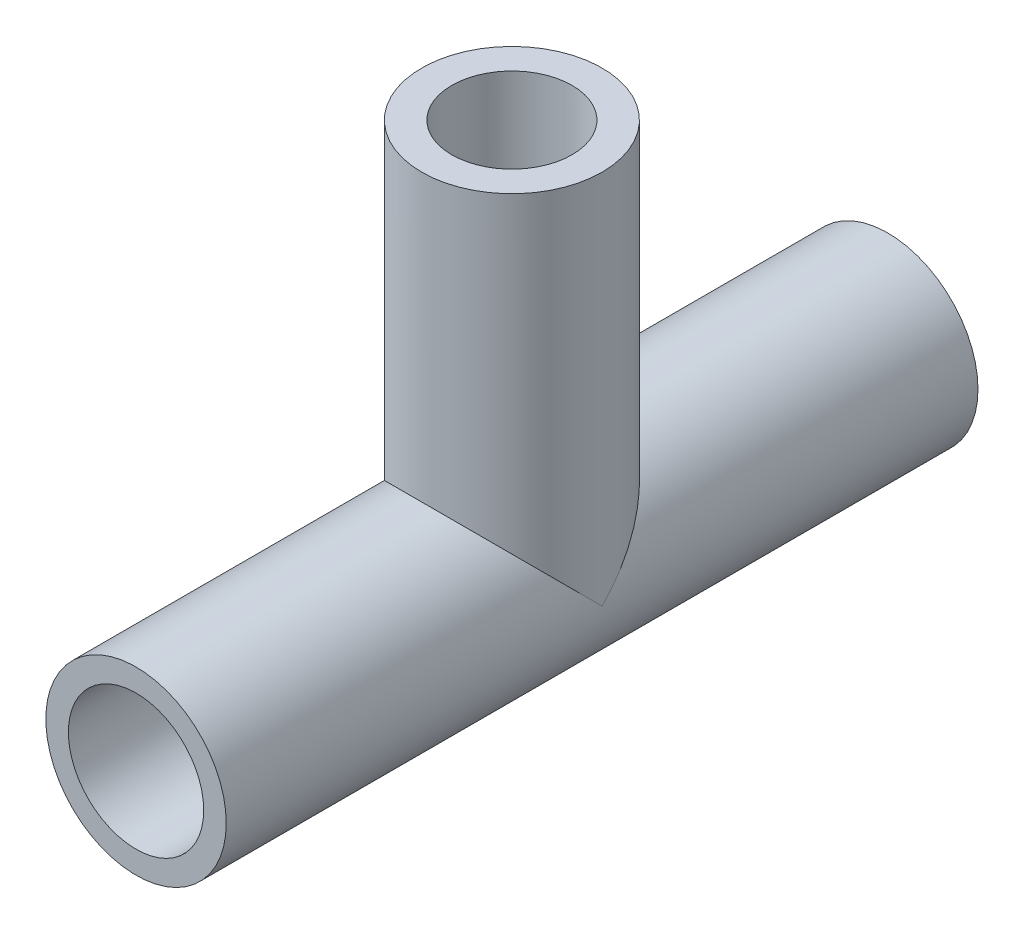
SolidWorks part; units mm, degrees
material "PVC Rígido"
ref_plane "Alzado" through (0, 0, 0) normal (0, 0, 1) x (1, 0, 0)
ref_plane "Planta" through (0, 0, 0) normal (0, 1, 0) x (1, 0, 0)
ref_plane "Vista lateral" through (0, 0, 0) normal (1, 0, 0) x (0, 0, -1)
sketch "Croquis1" plane through (0, 0, 0) normal (0, 0, 1) x (1, 0, 0)
  circle A0 centre (0, 0) radius 6
  circle A1 centre (0, 0) radius 4.5
  dimension "D1" = 12
  dimension "D2" = 9
extrude "Saliente-Extruir1" add sketch "Croquis1" along normal mid plane 50
sketch "Croquis2" plane through (0, 0, 0) normal (0, 1, 0) x (1, 0, 0)
  circle A0 centre (0, 0) radius 6
  circle A1 centre (0, 0) radius 4
  dimension "D1" = 12
  dimension "D2" = 8
extrude "Saliente-Extruir2" add sketch "Croquis2" along normal blind 25
sketch "Croquis3" plane through (0, 0, 25) normal (0, 0, 1) x (1, 0, 0)
  circle A0 centre (0, 0) radius 4.5
  dimension "D1" = 9
extrude "Cortar-Extruir1" cut sketch "Croquis3" against normal through all
